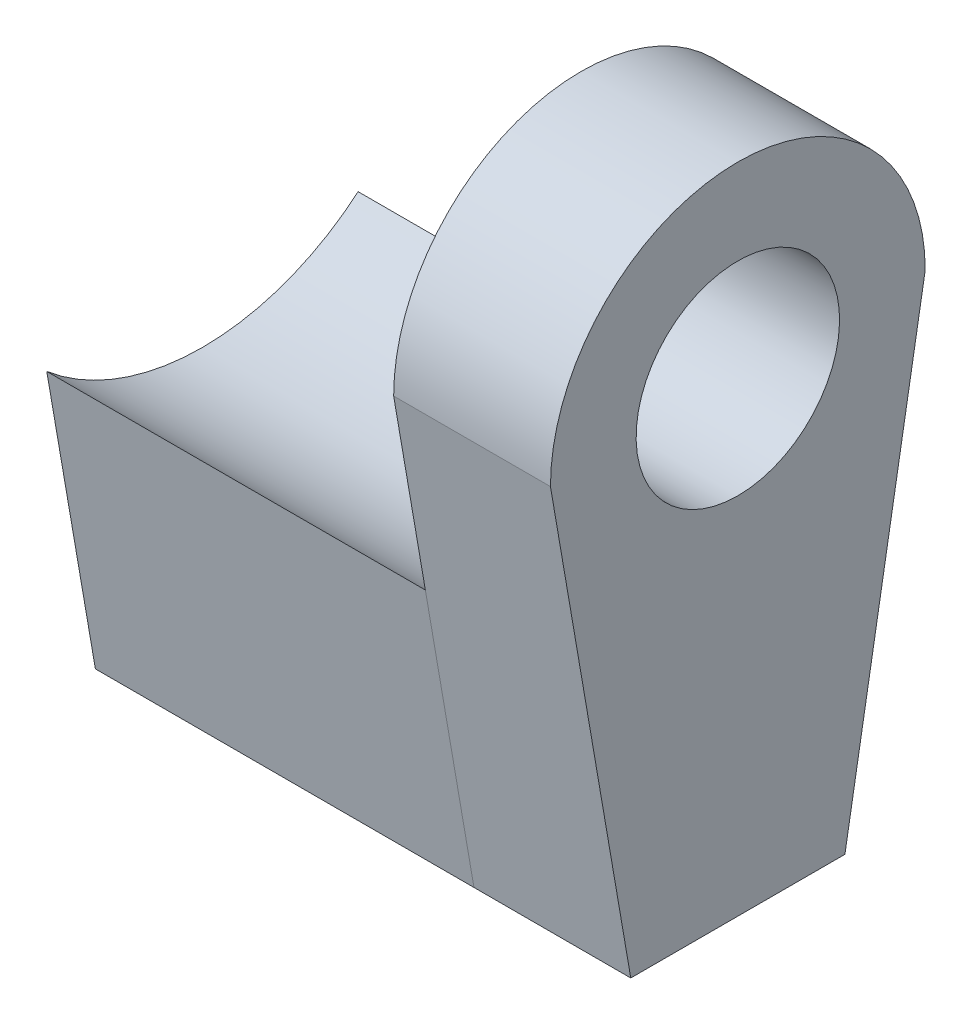
SolidWorks part; units mm, degrees
ref_plane "Front Plane" through (0, 0, 0) normal (0, 0, 1) x (1, 0, 0)
ref_plane "Top Plane" through (0, 0, 0) normal (0, 1, 0) x (1, 0, 0)
ref_plane "Right Plane" through (0, 0, 0) normal (1, 0, 0) x (0, 0, -1)
sketch "Sketch1" plane through (0, 0, 0) normal (1, 0, 0) x (0, 0, -1)
  line L0 (2, -8.7) -> (3.5, 0)
  line L5 (-2, -8.7) -> (2, -8.7)
  line L7 (-3.5, 0) -> (-2, -8.7)
  circle A0 centre (0, 0) radius 1.9
  arc A1 (3.5, 0) -> (-3.5, 0) centre (0, 0) ccw
  circle A3 centre (0, 0) radius 3.5 construction
  point P5 (0, -8.7)
  point P16 (2.51, 0)
  dimension "D1" = 3.8
  dimension "D3" = 8.7
  dimension "D4" = 4
  dimension "D2" = 1.6
extrude "Boss-Extrude1" add sketch "Sketch1" along normal blind 25
sketch "Sketch2" plane through (25, 0, 0) normal (1, 0, 0) x (0, 0, -1)
  line L0 (-2, -8.7) -> (2, -8.7)
  line L1 (2, -8.7) -> (2.9079, -3.4343)
  line L2 (2, -8.7) -> (3.5, 0) construction
  line L3 (-2.9079, -3.4343) -> (-2, -8.7)
  line L4 (-3.5, 0) -> (-2, -8.7) construction
  arc A0 (-1.9, 0) -> (1.9, 0) centre (0, 0) ccw construction
  circle A1 centre (0, 0) radius 1.9 construction
  arc A2 (-2.9079, -3.4343) -> (2.9079, -3.4343) centre (0, 0) ccw
  arc A4 (-4.5, 0) -> (4.5, 0) centre (0, 0) ccw construction
  dimension "D1" = 4.5
extrude "Boss-Extrude2" add sketch "Sketch2" along normal blind 51
sketch "Sketch3" plane through (76, 0, 0) normal (1, 0, 0) x (0, 0, -1)
  line L0 (-3.5, 0) -> (-2, -8.7)
  line L1 (-2, -8.7) -> (2, -8.7)
  line L2 (2, -8.7) -> (3.5, 0)
  circle A0 centre (0, 0) radius 1.51
  arc A1 (-3.5, 0) -> (3.5, 0) centre (0, 0) cw
  arc A2 (3.5, 0) -> (-3.5, 0) centre (0, 0) ccw construction
extrude "Boss-Extrude3" add sketch "Sketch3" along normal blind 25
sketch "Sketch7" plane through (101, 0, 0) normal (1, 0, 0) x (0, 0, -1)
  circle A0 centre (0, 0) radius 1.9
  dimension "D1" = 3.8
extrude "Cut-Extrude4" cut sketch "Sketch7" against normal through all
sketch "Sketch5" plane through (78.9289, 16.9, 1.27) normal (1, 0, 0) x (0, 0, 1)
  line L1 (-7.7604, 12.3275) -> (5.2204, 12.3275)
  line L2 (-7.7604, 12.3275) -> (-7.7604, 29.5235)
  line L3 (-7.7604, 29.5235) -> (5.2204, 29.5235)
  line L4 (5.2204, 12.3275) -> (5.2204, 29.5235)
  line L5 (-7.7604, 12.3275) -> (5.2204, 29.5235) construction
  line L6 (-7.7604, 29.5235) -> (5.2204, 12.3275) construction
  point P0 (-1.27, 20.9255)
extrude "Cut-Extrude2" cut sketch "Sketch5" along normal through all
sketch "Sketch6" plane through (68.9289, 16.9, 1.27) normal (1, 0, 0) x (0, 0, 1)
  line L1 (-7.7784, 12.3523) -> (5.2384, 12.3523)
  line L2 (-7.7784, 12.3523) -> (-7.7784, 28.9265)
  line L3 (-7.7784, 28.9265) -> (5.2384, 28.9265)
  line L4 (5.2384, 12.3523) -> (5.2384, 28.9265)
  line L5 (-7.7784, 12.3523) -> (5.2384, 28.9265) construction
  line L6 (-7.7784, 28.9265) -> (5.2384, 12.3523) construction
  point P0 (-1.27, 20.6394)
extrude "Cut-Extrude3" cut sketch "Sketch6" against normal through all
